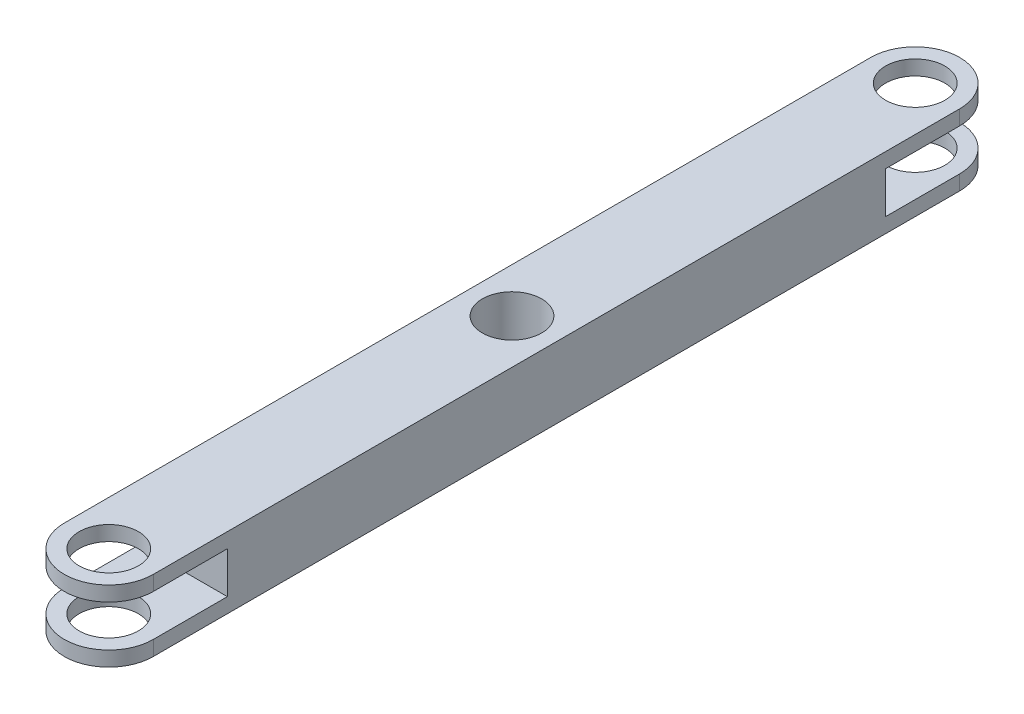
SolidWorks part; units mm, degrees
ref_plane "Alzado" through (0, 0, 0) normal (0, 0, 1) x (1, 0, 0)
ref_plane "Planta" through (0, 0, 0) normal (0, 1, 0) x (1, 0, 0)
ref_plane "Vista lateral" through (0, 0, 0) normal (1, 0, 0) x (0, 0, -1)
sketch "Croquis1" plane through (0, 0, 0) normal (0, 1, 0) x (1, 0, 0)
  line L0 (0, -34) -> (0, 34) construction
  line L1 (-3.75, 34) -> (-3.75, -34)
  line L3 (3.75, -34) -> (3.75, 34)
  arc A0 (3.75, 34) -> (-3.75, 34) centre (0, 34) ccw
  arc A1 (-3.75, -34) -> (3.75, -34) centre (0, -34) ccw
  circle A2 centre (0, 34) radius 2.5
  circle A3 centre (0, -34) radius 2.5
  circle A4 centre (0, 0) radius 2.5
  point P4 (0, 0)
  dimension "D2" = 5
  dimension "D1" = 68
  dimension "D3" = 7.5
extrude "Saliente-Extruir1" add sketch "Croquis1" along normal blind 6
sketch "Croquis2" plane through (0, 0, 0) normal (1, 0, 0) x (0, 0, -1)
  line L0 (-40, 4.75) -> (-40, 1.25)
  line L2 (-40, 1.25) -> (-27.75, 1.25)
  line L3 (-27.75, 1.25) -> (-27.75, 4.75)
  line L4 (-27.75, 4.75) -> (-40, 4.75)
  line L5 (0, 0) -> (0, 3) construction
  line L6 (-34, 0) -> (34, 0) construction
  line L7 (0, 3) -> (-40, 3) construction
  line L9 (40, 4.75) -> (40, 1.25)
  line L10 (40, 1.25) -> (27.75, 1.25)
  line L11 (27.75, 1.25) -> (27.75, 4.75)
  line L12 (27.75, 4.75) -> (40, 4.75)
  point P2 (-40, 3)
  dimension "D1" = 3.5
  dimension "D2" = 3
  dimension "D3" = 10
  dimension "D4" = 40
extrude "Cortar-Extruir1" cut sketch "Croquis2" against normal mid plane 15
